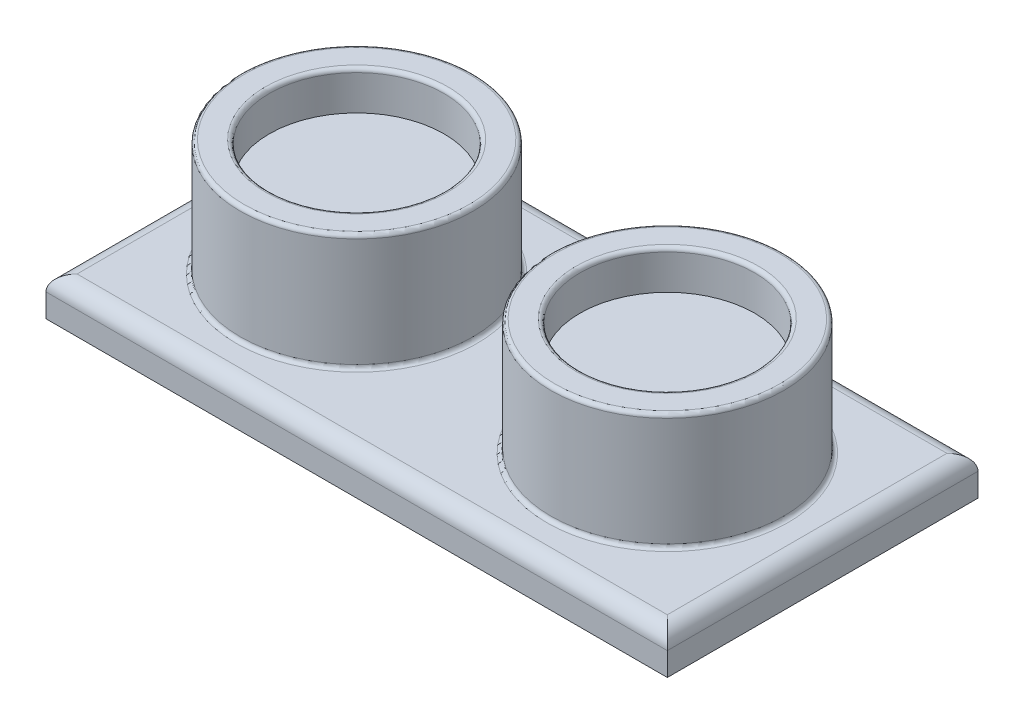
SolidWorks part; units mm, degrees
ref_plane "Front Plane" through (0, 0, 0) normal (0, 0, 1) x (1, 0, 0)
ref_plane "Top Plane" through (0, 0, 0) normal (0, 1, 0) x (1, 0, 0)
ref_plane "Right Plane" through (0, 0, 0) normal (1, 0, 0) x (0, 0, -1)
sketch "Sketch1" plane through (0, 0, 0) normal (0, 1, 0) x (1, 0, 0)
  line L1 (-40, 20) -> (40, 20)
  line L2 (-40, 20) -> (-40, -20)
  line L3 (-40, -20) -> (40, -20)
  line L4 (40, 20) -> (40, -20)
  line L5 (-40, 20) -> (40, -20) construction
  line L6 (-40, -20) -> (40, 20) construction
  point P0 (0, 0)
  dimension "D1" = 80
  dimension "D2" = 40
extrude "Boss-Extrude1" add sketch "Sketch1" along normal blind 5
sketch "Sketch2" plane through (0, 5, 0) normal (0, 1, 0) x (1, 0, 0)
  line L0 (-40, -20) -> (40, -20) construction
  line L1 (40, -20) -> (40, 20) construction
  line L2 (-40, 20) -> (-40, -20) construction
  circle A0 centre (-20, 0) radius 15
  circle A1 centre (20, 0) radius 15
  dimension "D1" = 30
  dimension "D4" = 30
  dimension "D2" = 20
  dimension "D3" = 20
  dimension "D5" = 20
  dimension "D6" = 20
extrude "Boss-Extrude2" add sketch "Sketch2" along normal blind 15
sketch "Sketch3" plane through (0, 20, 0) normal (0, 1, 0) x (1, 0, 0)
  circle A0 centre (-20, 0) radius 11.25
  circle A1 centre (20, 0) radius 11.25
  circle A2 centre (-20, 0) radius 15 construction
  circle A3 centre (20, 0) radius 15 construction
  dimension "D1" = 22.5
  dimension "D2" = 22.5
extrude "Cut-Extrude1" cut sketch "Sketch3" against normal blind 5
fillet "Fillet1" radius 2 4 edges at (40, 5, 0) (0, 5, 20) (-40, 5, 0) (0, 5, -20)
fillet "Fillet2" radius 0.5 6 edges at (-20, 20, 11.25) (20, 20, 11.25) (20, 20, 15) (-20, 20, 15) (20, 5, 15) (-20, 5, 15)
